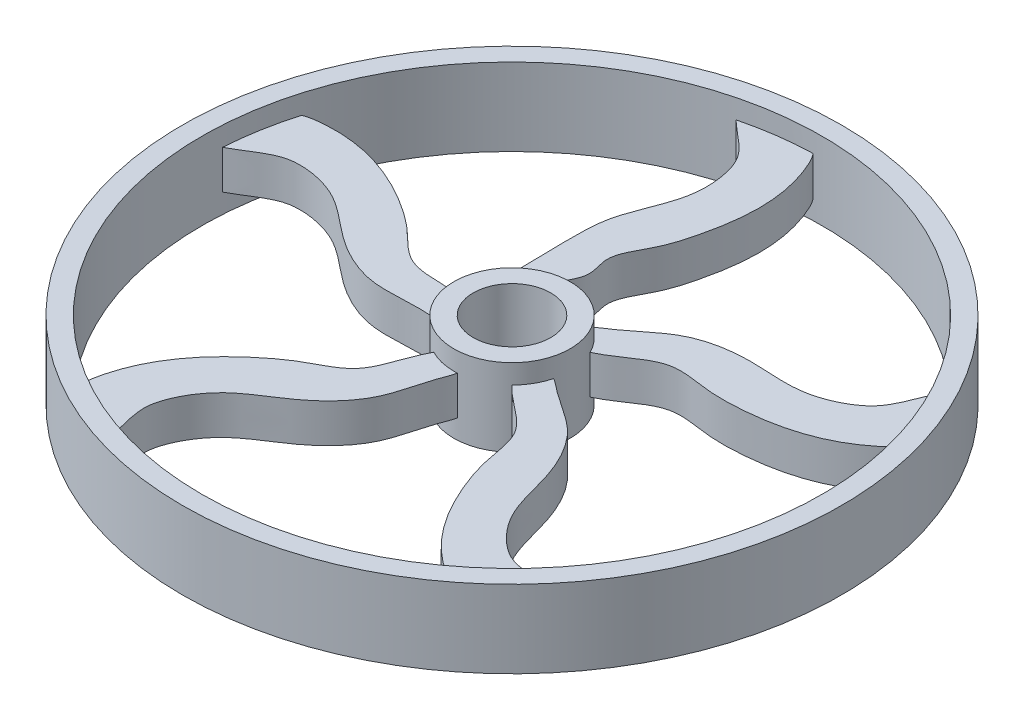
SolidWorks part; units mm, degrees
ref_plane "前视基准面" through (0, 0, 0) normal (0, 0, 1) x (1, 0, 0)
ref_plane "上视基准面" through (0, 0, 0) normal (0, 1, 0) x (1, 0, 0)
ref_plane "右视基准面" through (0, 0, 0) normal (1, 0, 0) x (0, 0, -1)
ref_plane "基准面1" through (0, 625, 0) normal (0, 1, 0) x (-1, 0, 0)
sketch "草图1" plane through (0, 625, 0) normal (0, 1, 0) x (-1, 0, 0)
  circle A0 centre (0, 0) radius 50
  circle A1 centre (0, 0) radius 75
  circle A2 centre (0, 0) radius 400
  circle A3 centre (0, 0) radius 425
  dimension "D1" = 100
  dimension "D2" = 150
  dimension "D3" = 800
  dimension "D4" = 850
extrude "凸台-拉伸1" add sketch "草图1" along normal mid plane 100 contours A3 A2 | A1 A0
sketch "草图2" plane through (0, 625, 0) normal (0, 1, 0) x (-1, 0, 0)
  line L0 (8.5754, 74.5081) -> (57.1692, 496.7209) construction
  line L1 (-0.1426, 75.8024) -> (65.5755, 38.0247) construction
  line L2 (65.5755, 38.0247) -> (65.7181, -37.7777) construction
  spline S0 degree 3 poles (88.15, -395.7874) (116.6639, -399.6865) (67.8474, -363.516) (46.0097, -335.4494) (39.2489, -283.1637) (54.1892, -240.5583) (73.0928, -192.8886) (73.5023, -138.9798) (71.0019, 12.524) (52.9946, -49.0004) (-8.3363, -53.8473) (55.5817, -69.6167) (11.9823, -111.1652) (33.7252, -153.2448) (6.8562, -191.0038) (-7.4687, -239.3974) (-18.6161, -302.8914) (-9.7645, -362.9074) (14.5448, -409.4526) (39.5087, -412.7874) (54.14, -411.2263) (65.3815, -410.223) (79.6735, -408.5224) (88.15, -395.7874) (116.6639, -399.6865) (67.8474, -363.516) knots -0.042613 -0.032137 -0.007845 0 0.046722 0.084693 0.14896 0.195899 0.235988 0.308134 0.431661 0.445278 0.495585 0.520132 0.575187 0.607841 0.66275 0.708382 0.77627 0.869367 0.90889 0.930743 0.946401 0.957387 0.967863 0.992155 1 1.046722 1.084693 1.14896 only from (101.6039, -397.2676) to (101.6039, -397.2676)
  spline S1 degree 3 poles (-349.1765, -206.1407) (-344.0729, -234.4638) (-324.7685, -176.8588) (-304.7757, -147.4193) (-257.4005, -124.819) (-211.4913, -125.9013) (-163.1651, -129.0049) (-103.4421, -117.1277) (-68.5723, -80.5908) (-27.7565, -57.2803) (-46.1516, -25.6581) (-77.0146, -37.3905) (-99.7192, -54.9368) (-137.0131, -76.4584) (-179.0975, -66.3162) (-230.1564, -66.5794) (-293.744, -76.0264) (-348.172, -102.8417) (-384.9172, -140.3622) (-380.3754, -165.1331) (-374.3693, -178.5662) (-369.9413, -188.9474) (-363.9074, -202.0144) (-349.1765, -206.1407) (-344.0729, -234.4638) (-324.7685, -176.8588) knots -0.045796 -0.034537 -0.008431 0 0.050212 0.091018 0.160084 0.210529 0.253612 0.331146 0.410552 0.439403 0.472325 0.49284 0.543461 0.578554 0.637564 0.686603 0.759562 0.859611 0.902086 0.925571 0.942398 0.954204 0.965463 0.991569 1 1.050212 1.091018 1.160084 only from (-346.4266, -219.3935) to (-346.4266, -219.3935)
  spline S2 degree 3 poles (-303.9529, 268.3856) (-329.3127, 254.7795) (-268.5617, 254.2208) (-234.3849, 244.3038) (-198.251, 206.2312) (-185.0936, 162.2345) (-173.1117, 115.3145) (-143.3604, 62.1849) (-97.8364, 40.3122) (-63.054, 8.6974) (-38.6639, 35.964) (-59.3593, 61.691) (-83.063, 77.8622) (-115.0556, 106.6802) (-118.4146, 149.839) (-134.443, 198.3176) (-163.0773, 255.8737) (-205.3994, 299.3515) (-252.4383, 322.7037) (-274.5934, 310.7295) (-285.513, 300.8664) (-294.0178, 293.4471) (-304.5807, 283.6706) (-303.9529, 268.3856) (-329.3127, 254.7795) (-268.5617, 254.2208) knots -0.045796 -0.034537 -0.008431 0 0.050212 0.091018 0.160084 0.210529 0.253612 0.331146 0.410552 0.439403 0.472325 0.49284 0.543461 0.578554 0.637564 0.686603 0.759562 0.859611 0.902086 0.925571 0.942398 0.954204 0.965463 0.991569 1 1.050212 1.091018 1.160084 only from (-315.7073, 261.675) to (-315.7073, 261.675)
  spline S3 degree 3 poles (161.3232, 372.0121) (140.5464, 391.9262) (158.7883, 333.9759) (159.9178, 298.4073) (134.8746, 252.2769) (97.0971, 226.1677) (56.1761, 200.2732) (14.8405, 155.56) (8.1061, 105.5051) (-11.2131, 62.6556) (22.256, 47.8851) (40.3286, 75.5176) (48.3835, 103.0583) (65.9048, 142.3904) (105.9132, 158.9218) (147.066, 189.1464) (192.9567, 234.1651) (221.2283, 287.8511) (228.9017, 339.804) (210.6673, 357.1745) (197.9125, 364.5118) (188.2283, 370.3077) (175.6662, 377.3325) (161.3232, 372.0121) (140.5464, 391.9262) (158.7883, 333.9759) knots -0.045796 -0.034537 -0.008431 0 0.050212 0.091018 0.160084 0.210529 0.253612 0.331146 0.410552 0.439403 0.472325 0.49284 0.543461 0.578554 0.637564 0.686603 0.759562 0.859611 0.902086 0.925571 0.942398 0.954204 0.965463 0.991569 1 1.050212 1.091018 1.160084 only from (151.3088, 381.1175) to (151.3088, 381.1175)
  spline S4 degree 3 poles (403.6562, -38.4694) (416.1752, -12.5557) (366.6983, -47.8124) (333.2196, -59.8779) (281.6081, -50.3155) (245.1029, -22.4552) (207.8305, 8.4611) (152.5324, 33.9565) (102.8462, 24.8935) (56.124, 30.0259) (52.4189, -6.3694) (84.2837, -15.0185) (112.9656, -14.1687) (155.787, -18.6781) (183.8726, -51.6199) (225.3348, -81.4187) (282.3311, -111.1517) (342.1259, -121.4497) (393.9074, -112.6933) (404.7929, -89.9835) (407.8297, -75.5856) (410.3492, -64.5844) (413.1484, -50.4663) (403.6562, -38.4694) (416.1752, -12.5557) (366.6983, -47.8124) knots -0.045796 -0.034537 -0.008431 0 0.050212 0.091018 0.160084 0.210529 0.253612 0.331146 0.410552 0.439403 0.472325 0.49284 0.543461 0.578554 0.637564 0.686603 0.759562 0.859611 0.902086 0.925571 0.942398 0.954204 0.965463 0.991569 1 1.050212 1.091018 1.160084 only from (409.2213, -26.1314) to (409.2213, -26.1314)
extrude "凸台-拉伸2" add sketch "草图2" along normal mid plane 50
